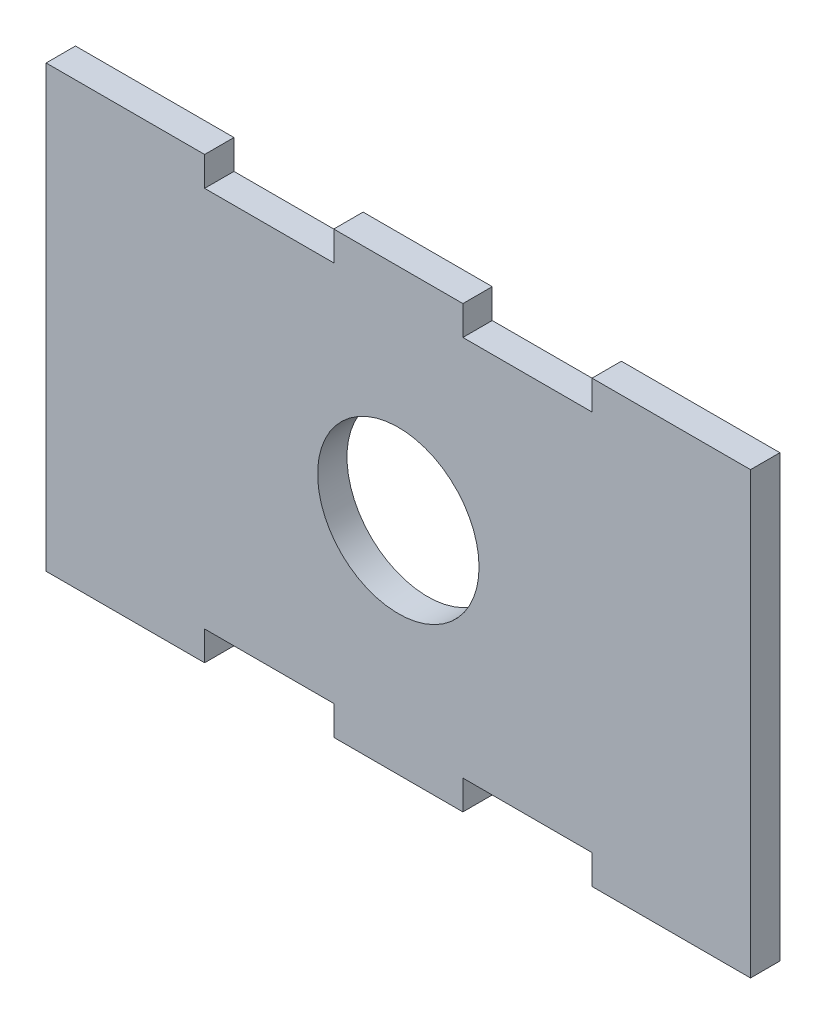
SolidWorks part; units mm, degrees
material "1060 Alloy"
ref_plane "Front Plane" through (0, 0, 0) normal (0, 0, 1) x (1, 0, 0)
ref_plane "Top Plane" through (0, 0, 0) normal (0, 1, 0) x (1, 0, 0)
ref_plane "Right Plane" through (0, 0, 0) normal (1, 0, 0) x (0, 0, -1)
sketch "Sketch1" plane through (0, 0, 0) normal (0, 0, 1) x (1, 0, 0)
  line L0 (-21.3759, 27.8611) -> (-21.3759, -3.1389) construction
  line L1 (-53.8759, 42.3611) -> (-32.2759, 42.3611)
  line L2 (-53.8759, 42.3611) -> (-53.8759, -17.6389)
  line L3 (-53.8759, -17.6389) -> (-32.2759, -17.6389)
  line L4 (42.1241, 42.3611) -> (42.1241, -17.6389)
  line L5 (-21.3759, -3.1389) -> (9.6241, -3.1389) construction
  line L6 (9.6241, -3.1389) -> (9.6241, 27.8611) construction
  line L7 (9.6241, 27.8611) -> (-21.3759, 27.8611) construction
  line L8 (-21.3759, 27.8611) -> (9.6241, -3.1389) construction
  line L9 (9.6241, 27.8611) -> (-21.3759, -3.1389) construction
  line L10 (20.5241, -17.6389) -> (20.5241, -13.6389)
  line L11 (20.5241, -13.6389) -> (2.9241, -13.6389)
  line L12 (2.9241, -13.6389) -> (2.9241, -17.6389)
  line L13 (-14.6759, -17.6389) -> (-14.6759, -13.6389)
  line L14 (-14.6759, -13.6389) -> (-32.2759, -13.6389)
  line L15 (-32.2759, -17.6389) -> (-32.2759, -13.6389)
  line L16 (20.5241, 42.3611) -> (20.5241, 38.3611)
  line L17 (20.5241, 38.3611) -> (2.9241, 38.3611)
  line L18 (2.9241, 38.3611) -> (2.9241, 42.3611)
  line L20 (-14.6759, 42.3611) -> (-14.6759, 38.3611)
  line L21 (-14.6759, 38.3611) -> (-32.2759, 38.3611)
  line L22 (-32.2759, 38.3611) -> (-32.2759, 42.3611)
  line L23 (-14.6759, 42.3611) -> (2.9241, 42.3611)
  line L24 (20.5241, 42.3611) -> (42.1241, 42.3611)
  line L25 (20.5241, -17.6389) -> (42.1241, -17.6389)
  line L26 (-14.6759, -17.6389) -> (2.9241, -17.6389)
  circle A1 centre (-5.8759, 12.3611) radius 11
  circle A2 centre (9.6241, -3.1389) radius 1.25
  circle A3 centre (9.6241, 27.8611) radius 1.25
  circle A4 centre (-21.3759, 27.8611) radius 1.25
  circle A5 centre (-21.3759, -3.1389) radius 1.25
  point P8 (14.7714, 12.3039)
  point P23 (0, 0)
  point P32 (0, 0)
  dimension "D5" = 96
  dimension "D6" = 22
  dimension "D8" = 2.5
  dimension "D9" = 2.5
  dimension "D11" = 2.5
  dimension "D17" = 2.5
  dimension "D1" = 60
  dimension "D3" = 48
  dimension "D4" = 30
  dimension "D7" = 15.5
  dimension "D10" = 31
  dimension "D12" = 31
  dimension "D13" = 15.5
  dimension "D14" = 15.5
  dimension "D15" = 31
  dimension "D16" = 31
  dimension "D18" = 15.5
  dimension "D22" = 4
extrude "Boss-Extrude1" add sketch "Sketch1" along normal blind 4 contours A1 | L18 L23 L20 L21 L22 L1 L2 L3 L15 L14 L13 L26 L12 L11 L10 L25 L4 L24 L16 L17
